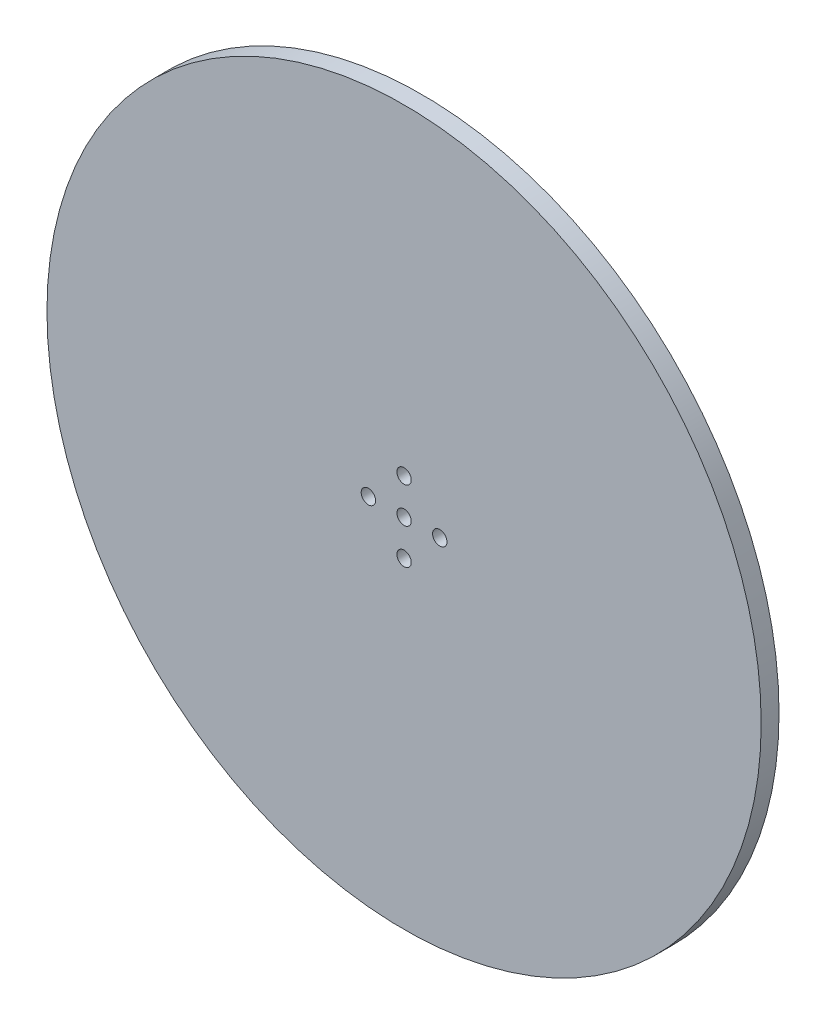
SolidWorks part; units mm, degrees
material "6061-T6 (SS)"
ref_plane "Front Plane" through (0, 0, 0) normal (0, 0, 1) x (1, 0, 0)
ref_plane "Top Plane" through (0, 0, 0) normal (0, 1, 0) x (1, 0, 0)
ref_plane "Right Plane" through (0, 0, 0) normal (1, 0, 0) x (0, 0, -1)
sketch "Sketch1" plane through (0, 0, 0) normal (0, 0, 1) x (1, 0, 0)
  circle A0 centre (0, 0) radius 127
  dimension "D1" = 254
extrude "Boss-Extrude1" add sketch "Sketch1" along normal blind 6.35
sketch "Sketch2" plane through (0, 0, 6.35) normal (0, 0, 1) x (1, 0, 0)
  circle A0 centre (0, 0) radius 2.54
  dimension "D1" = 5.08
extrude "Cut-Extrude1" cut sketch "Sketch2" against normal through all
sketch "Sketch4" plane through (0, 0, 6.35) normal (0, 0, 1) x (1, 0, 0)
  line L0 (0, 0) -> (0, 12.7) construction
  dimension "D1" = 12.7
hole_wizard "#10 Clearance Hole1" positions "Sketch6" profile "Sketch5" hole size "#10" standard "Ansi Inch"
sketch "Sketch6" plane through (0, 0, 6.35) normal (0, 0, 1) x (1, 0, 0)
  point P1 (0, 12.7)
sketch "Sketch5" plane through (0, 12.7, 6.35) normal (1, 0, 0) x (0, -1, 0)
  line L0 (0, 0) -> (0, 11.0588)
  line L1 (0, 11.0588) -> (2.5527, 9.525)
  line L2 (2.5527, 9.525) -> (2.5527, 0)
  line L5 (2.5527, 0) -> (0, 0)
  line L10 (0, 11.0588) -> (-2.5527, 9.525) construction
  line L11 (0, -6.35) -> (0, 107.95) construction
  dimension "Hole Dia." = 5.1054
  dimension "Hole Depth" = 9.525
  dimension "Drill Angle" = 118
pattern_circular "CirPattern1" count 4 over 360 about axis through (0, 0, 0) along (0, 0, 1) of "#10 Clearance Hole1"
